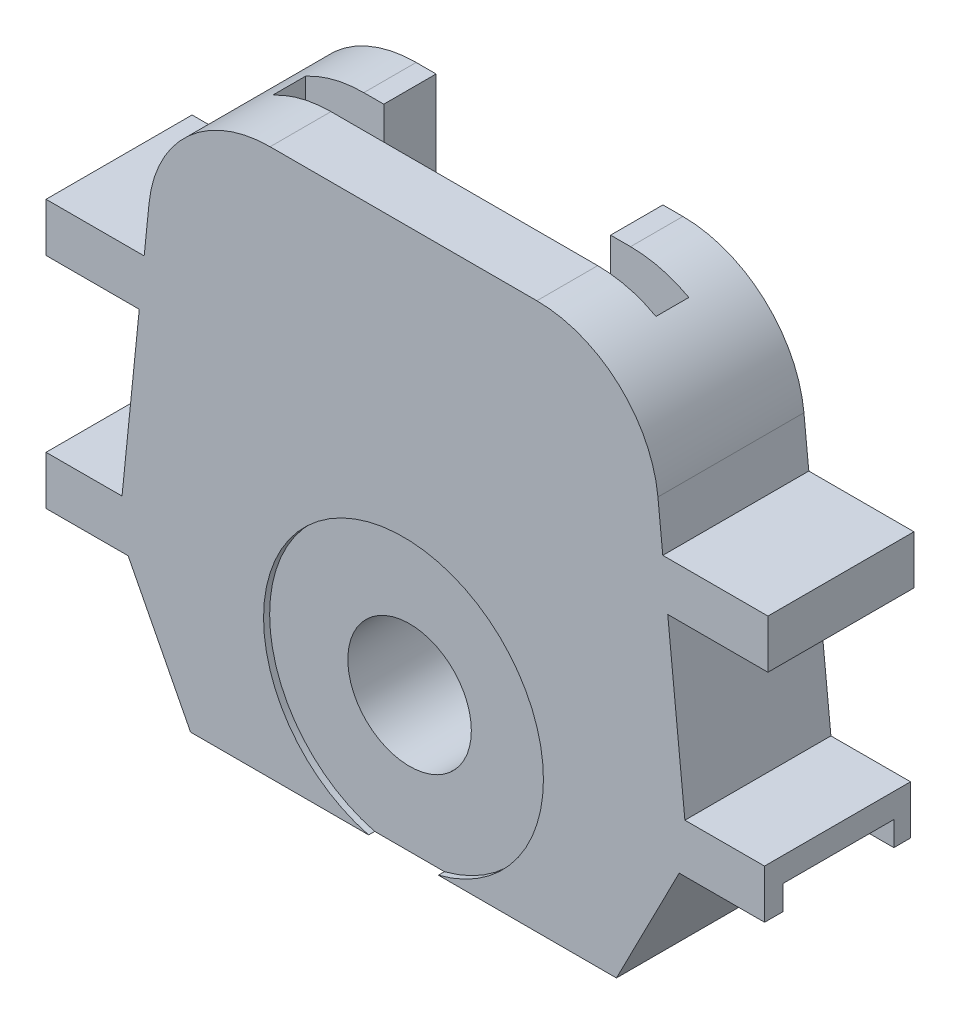
SolidWorks part; units mm, degrees
ref_plane "Front Plane" through (0, 0, 0) normal (0, 0, 1) x (1, 0, 0)
ref_plane "Top Plane" through (0, 0, 0) normal (0, 1, 0) x (1, 0, 0)
ref_plane "Right Plane" through (0, 0, 0) normal (1, 0, 0) x (0, 0, -1)
sketch "Sketch2" plane through (0, 0, 0) normal (0, 0, 1) x (1, 0, 0)
  line L0 (-26.6527, 24.7995) -> (-27.0526, 20.8472)
  line L1 (-16.7035, 33.7929) -> (5.2179, 33.7929)
  line L3 (-23.2428, -11.1376) -> (11.7572, -11.1376)
  line L5 (-28.3709, -1.1522) -> (-23.2428, -11.1376)
  line L6 (15.1671, 24.7995) -> (15.567, 20.8472)
  line L7 (16.9145, -1.095) -> (11.7572, -11.1376)
  line L8 (-5.7428, 33.7929) -> (-5.7428, -11.1376) construction
  line L14 (-28.8738, 2.8472) -> (-28.8738, 20.8472) construction
  line L16 (-28.8738, 2.8472) -> (-35.118, 2.8393)
  line L17 (23.9316, -1.0861) -> (16.9145, -1.095)
  line L18 (23.9316, -1.0861) -> (23.9266, 2.9139)
  line L19 (-35.1129, -1.1607) -> (-35.118, 2.8393)
  line L20 (23.9266, 2.9139) -> (17.3823, 2.9056)
  line L21 (-1028.8738, 20.8472) -> (-27.0526, 20.8472) construction
  line L22 (-35.118, 2.8393) -> (-35.118, 30.8551) construction
  line L23 (-27.4573, 16.8472) -> (-28.8738, 2.8472)
  line L25 (-28.3709, -1.1522) -> (-35.1129, -1.1607)
  line L26 (-35.118, 16.8472) -> (-27.4573, 16.8472)
  line L27 (-35.118, 16.8472) -> (-35.118, 20.8472)
  line L28 (-35.118, 20.8472) -> (-27.0526, 20.8472)
  line L29 (24.2077, 16.8472) -> (24.2077, 20.8472)
  line L30 (15.9717, 16.8472) -> (17.3823, 2.9056)
  line L31 (15.567, 20.8472) -> (1002.5829, 20.8472) construction
  line L32 (15.567, 20.8472) -> (24.2077, 20.8472)
  line L33 (15.9717, 16.8472) -> (24.2077, 16.8472)
  circle A0 centre (-5.7428, 0) radius 5.075
  arc A1 (15.1671, 24.7995) -> (5.2179, 33.7929) centre (5.2179, 23.7929) ccw
  arc A2 (-16.7035, 33.7929) -> (-26.6527, 24.7995) centre (-16.7035, 23.7929) ccw
  point P31 (14.2572, 33.7929)
  point P34 (-25.7428, 33.7929)
  dimension "D3" = 10.15
  dimension "D7" = 10
  dimension "D1" = 35
  dimension "D2" = 4
  dimension "D4" = 40
  dimension "D5" = 4
  dimension "D6" = 18
extrude "Boss-Extrude1" add sketch "Sketch2" along normal blind 12
sketch "Sketch3" plane through (0.0014, -1.1163, 0) normal (0.0013, -1, 0) x (1, 0.0013, 0)
  line L0 (-35.1144, 12) -> (-35.1144, 0) construction
  line L1 (-35.1144, 10.5) -> (-29.1144, 10.5)
  line L2 (-35.1144, 10.5) -> (-35.1144, 8.5)
  line L4 (-29.1144, 10.5) -> (-29.1144, 8.5)
  line L10 (-35.1144, 3.5238) -> (-35.1144, 1.4619)
  line L11 (-35.1144, 1.4619) -> (-29.1144, 1.4619)
  line L12 (-29.1144, 3.5238) -> (-29.1144, 1.4619)
  line L13 (17.9302, 10.5) -> (23.9302, 10.5)
  line L14 (17.9302, 10.5) -> (17.9302, 8.5)
  line L16 (23.9302, 10.5) -> (23.9302, 8.5)
  line L22 (17.9302, 3.4381) -> (17.9302, 1.3762)
  line L23 (17.9302, 1.3762) -> (23.9302, 1.3762)
  line L24 (23.9302, 3.4381) -> (23.9302, 1.3762)
  line L25 (23.9302, 12) -> (23.9302, 0) construction
  line L26 (-35.1144, 12) -> (-28.3724, 12) construction
  line L27 (16.9131, 12) -> (23.9302, 12) construction
  line L28 (-35.1144, 8.5) -> (-35.1144, 3.5238)
  line L29 (-29.1144, 3.5238) -> (-29.1144, 8.5)
  line L31 (23.9302, 3.4381) -> (23.9302, 8.5)
  line L32 (17.9302, 8.5) -> (17.9302, 3.4381)
  dimension "D1" = 6
  dimension "D3" = 1.5
  dimension "D6" = 6
  dimension "D8" = 1.5
extrude "Cut-Extrude1" cut sketch "Sketch3" against normal blind 2
ref_plane "Plane1" through (0, 0, 7) normal (0, 0, 1) x (1, 0, 0)
sketch "Sketch4" plane through (0, 0, 7) normal (0, 0, 1) x (1, 0, 0)
  line L0 (-5.7428, 33.7929) -> (-5.7428, -11.1376) construction
  line L1 (5.2179, 33.7929) -> (-16.7035, 33.7929) construction
  line L2 (-23.2428, -11.1376) -> (11.7572, -11.1376) construction
  line L3 (-21.4928, 33.7929) -> (10.0072, 33.7929)
  line L4 (-21.4928, 33.7929) -> (-21.4928, 7.2929)
  line L5 (10.0072, 33.7929) -> (10.0072, 7.2929)
  line L6 (-21.4928, 7.2929) -> (10.0072, 7.2929)
  line L7 (-21.4928, 33.7929) -> (10.0072, 7.2929) construction
  line L8 (10.0072, 33.7929) -> (-21.4928, 7.2929) construction
  point P7 (-5.7428, 20.5429)
  dimension "D1" = 26.5
  dimension "D2" = 31.5
extrude "Cut-Extrude2" cut sketch "Sketch4" against normal blind 2.7
sketch "Sketch5" plane through (0, 0, 0) normal (0, 0, -1) x (-1, 0, 0)
  line L0 (5.7428, 33.7929) -> (5.7428, -11.1376) construction
  line L1 (-5.2179, 33.7929) -> (16.7035, 33.7929) construction
  line L2 (23.2428, -11.1376) -> (-11.7572, -11.1376) construction
  line L4 (-3.5775, 8.7929) -> (15.0631, 8.7929)
  line L5 (-3.5775, 8.7929) -> (-3.5775, 33.7929)
  line L6 (-3.5775, 33.7929) -> (15.0631, 33.7929)
  line L7 (15.0631, 8.7929) -> (15.0631, 33.7929)
  line L8 (-3.5775, 8.7929) -> (15.0631, 33.7929) construction
  line L9 (-3.5775, 33.7929) -> (15.0631, 8.7929) construction
  point P6 (5.7428, 21.2929)
  dimension "D1" = 25
extrude "Cut-Extrude3" cut sketch "Sketch5" against normal up to next
sketch "Sketch6" plane through (0, 0, 12) normal (0, 0, 1) x (1, 0, 0)
  line L0 (-10.8178, 0) -> (-0.6678, 0) construction
  line L2 (-5.7428, 5.075) -> (-5.7428, -5.075) construction
  circle A1 centre (-5.7428, 0) radius 5.075 construction
  circle A2 centre (-5.7428, 0) radius 11.5
  dimension "D1" = 23
extrude "Cut-Extrude4" cut sketch "Sketch6" against normal blind 0.5
